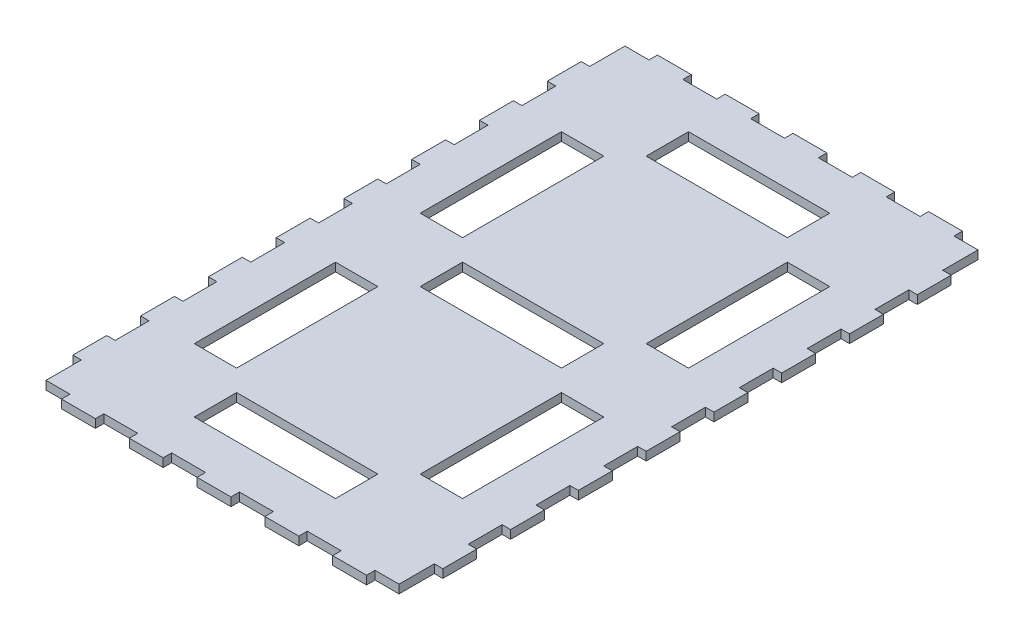
SolidWorks part; units mm, degrees
ref_plane "Front Plane" through (0, 0, 0) normal (0, 0, 1) x (1, 0, 0)
ref_plane "Top Plane" through (0, 0, 0) normal (0, 1, 0) x (1, 0, 0)
ref_plane "Right Plane" through (0, 0, 0) normal (1, 0, 0) x (0, 0, -1)
sketch "Sketch3" plane through (0, 0, 0) normal (0, 1, 0) x (1, 0, 0)
  line L231 (-62.5, -102.5) -> (62.5, -102.5)
  line L232 (-62.5, -102.5) -> (-62.5, 102.5)
  line L233 (-62.5, 102.5) -> (62.5, 102.5)
  line L234 (62.5, -102.5) -> (62.5, 102.5)
  line L235 (-62.5, -102.5) -> (62.5, 102.5) construction
  line L236 (-62.5, 102.5) -> (62.5, -102.5) construction
  point P66 (0, 0)
  dimension "D3" = 205
  dimension "D4" = 125
extrude "Boss-Extrude1" add sketch "Sketch3" along normal blind 3
sketch "Sketch4" plane through (0, 3, 0) normal (0, 1, 0) x (1, 0, 0)
  line L0 (62.5, 102.5) -> (-62.5, 102.5) construction
  line L5 (-32.5, 65) -> (-47.5, 65)
  line L6 (-25, 80) -> (-62.5, 80)
  line L7 (-32.5, 65) -> (-32.5, 15)
  line L8 (-32.5, 15) -> (-47.5, 15)
  line L17 (-25, 87.5) -> (25, 87.5)
  line L18 (-47.5, 65) -> (-47.5, 15)
  line L19 (-25, 87.5) -> (-25, 72.5)
  line L20 (-25, 72.5) -> (25, 72.5)
  line L21 (25, 87.5) -> (25, 72.5)
  line L22 (-62.5, 102.5) -> (-62.5, -102.5) construction
  line L23 (25, 80) -> (62.5, 80)
  line L24 (62.5, -102.5) -> (62.5, 102.5) construction
  line L25 (47.5, 65) -> (47.5, 15)
  line L26 (47.5, 65) -> (32.5, 65)
  line L27 (32.5, 65) -> (32.5, 15)
  line L28 (47.5, 15) -> (32.5, 15)
  line L30 (-25, 7.5) -> (-25, -7.5)
  line L31 (-25, 7.5) -> (25, 7.5)
  line L32 (25, 7.5) -> (25, -7.5)
  line L33 (-25, -7.5) -> (25, -7.5)
  line L34 (-25, -72.5) -> (-25, -87.5)
  line L35 (-25, -72.5) -> (25, -72.5)
  line L36 (25, -72.5) -> (25, -87.5)
  line L37 (-25, -87.5) -> (25, -87.5)
  line L38 (47.5, -15) -> (47.5, -65)
  line L39 (47.5, -15) -> (32.5, -15)
  line L40 (32.5, -15) -> (32.5, -65)
  line L41 (47.5, -65) -> (32.5, -65)
  line L42 (-32.5, -15) -> (-32.5, -65)
  line L43 (-32.5, -15) -> (-47.5, -15)
  line L44 (-47.5, -15) -> (-47.5, -65)
  line L45 (-32.5, -65) -> (-47.5, -65)
  point P16 (0, 87.5)
  dimension "D1" = 15
  dimension "D2" = 37.5
  dimension "D3" = 37.5
  dimension "D4" = 15
  dimension "D6" = 95
  dimension "D7" = 15
  dimension "D8" = 7.5
  dimension "D11" = 15
  dimension "D12" = 7.5
  dimension "D13" = 15
  dimension "D5" = 3
  dimension "D9" = 2
  dimension "D10" = 2
extrude "Cut-Extrude1" cut sketch "Sketch4" against normal blind 6 contours L5 L18 L8 L7 | L28 L25 L26 L27 | L30 L33 L32 L31 | L45 L42 L43 L44 | L41 L38 L39 L40 | L19 L17 L21 L20 | L35 L36 L37 L34
sketch "Sketch5" plane through (0, 3, 0) normal (0, 1, 0) x (1, 0, 0)
  line L0 (62.5, 102.5) -> (-62.5, 102.5) construction
  line L1 (-54, 102.5) -> (-42, 102.5)
  line L2 (-54, 102.5) -> (-54, 105.5)
  line L3 (-54, 105.5) -> (-42, 105.5)
  line L4 (-42, 102.5) -> (-42, 105.5)
  line L5 (-30, 102.5) -> (-30, 105.5)
  line L6 (-30, 102.5) -> (-18, 102.5)
  line L7 (-18, 102.5) -> (-18, 105.5)
  line L8 (-30, 105.5) -> (-18, 105.5)
  line L9 (-6, 102.5) -> (-6, 105.5)
  line L10 (-6, 102.5) -> (6, 102.5)
  line L11 (6, 102.5) -> (6, 105.5)
  line L12 (-6, 105.5) -> (6, 105.5)
  line L13 (18, 102.5) -> (18, 105.5)
  line L14 (18, 102.5) -> (30, 102.5)
  line L15 (30, 102.5) -> (30, 105.5)
  line L16 (18, 105.5) -> (30, 105.5)
  line L17 (42, 102.5) -> (42, 105.5)
  line L18 (42, 102.5) -> (54, 102.5)
  line L19 (54, 102.5) -> (54, 105.5)
  line L20 (42, 105.5) -> (54, 105.5)
  line L41 (-62.5, 102.5) -> (-62.5, -102.5) construction
  line L43 (62.5, -102.5) -> (62.5, 102.5) construction
  line L44 (-62.5, 90) -> (-65.5, 90)
  line L45 (-62.5, 90) -> (-62.5, 78)
  line L46 (-62.5, 78) -> (-65.5, 78)
  line L47 (-65.5, 90) -> (-65.5, 78)
  line L48 (65.5, 90) -> (65.5, 78)
  line L49 (65.5, 90) -> (62.5, 90)
  line L50 (62.5, 90) -> (62.5, 78)
  line L51 (65.5, 78) -> (62.5, 78)
  line L52 (65.5, 66) -> (65.5, 54)
  line L53 (65.5, 66) -> (62.5, 66)
  line L54 (62.5, 66) -> (62.5, 54)
  line L55 (65.5, 54) -> (62.5, 54)
  line L56 (65.5, 42) -> (65.5, 30)
  line L57 (65.5, 42) -> (62.5, 42)
  line L58 (62.5, 42) -> (62.5, 30)
  line L59 (65.5, 30) -> (62.5, 30)
  line L60 (65.5, 18) -> (65.5, 6)
  line L61 (65.5, 18) -> (62.5, 18)
  line L62 (62.5, 18) -> (62.5, 6)
  line L63 (65.5, 6) -> (62.5, 6)
  line L64 (65.5, -6) -> (65.5, -18)
  line L65 (65.5, -6) -> (62.5, -6)
  line L66 (62.5, -6) -> (62.5, -18)
  line L67 (65.5, -18) -> (62.5, -18)
  line L68 (65.5, -30) -> (65.5, -42)
  line L69 (65.5, -30) -> (62.5, -30)
  line L70 (62.5, -30) -> (62.5, -42)
  line L71 (65.5, -42) -> (62.5, -42)
  line L72 (65.5, -54) -> (65.5, -66)
  line L73 (65.5, -54) -> (62.5, -54)
  line L74 (62.5, -54) -> (62.5, -66)
  line L75 (65.5, -66) -> (62.5, -66)
  line L76 (65.5, -78) -> (65.5, -90)
  line L77 (65.5, -78) -> (62.5, -78)
  line L78 (62.5, -78) -> (62.5, -90)
  line L79 (65.5, -90) -> (62.5, -90)
  line L80 (-62.5, 66) -> (-62.5, 54)
  line L81 (-62.5, 66) -> (-65.5, 66)
  line L82 (-65.5, 66) -> (-65.5, 54)
  line L83 (-62.5, 54) -> (-65.5, 54)
  line L84 (-62.5, 42) -> (-62.5, 30)
  line L85 (-62.5, 42) -> (-65.5, 42)
  line L86 (-65.5, 42) -> (-65.5, 30)
  line L87 (-62.5, 30) -> (-65.5, 30)
  line L88 (-62.5, 18) -> (-62.5, 6)
  line L89 (-62.5, 18) -> (-65.5, 18)
  line L90 (-65.5, 18) -> (-65.5, 6)
  line L91 (-62.5, 6) -> (-65.5, 6)
  line L92 (-62.5, -6) -> (-62.5, -18)
  line L93 (-62.5, -6) -> (-65.5, -6)
  line L94 (-65.5, -6) -> (-65.5, -18)
  line L95 (-62.5, -18) -> (-65.5, -18)
  line L96 (-62.5, -30) -> (-62.5, -42)
  line L97 (-62.5, -30) -> (-65.5, -30)
  line L98 (-65.5, -30) -> (-65.5, -42)
  line L99 (-62.5, -42) -> (-65.5, -42)
  line L100 (-62.5, -54) -> (-62.5, -66)
  line L101 (-62.5, -54) -> (-65.5, -54)
  line L102 (-65.5, -54) -> (-65.5, -66)
  line L103 (-62.5, -66) -> (-65.5, -66)
  line L104 (-62.5, -78) -> (-62.5, -90)
  line L105 (-62.5, -78) -> (-65.5, -78)
  line L106 (-65.5, -78) -> (-65.5, -90)
  line L107 (-62.5, -90) -> (-65.5, -90)
  line L108 (-62.5, 6) -> (-62.5, -6)
  line L109 (-54, -105.5) -> (-54, -102.5)
  line L110 (-54, -105.5) -> (-42, -105.5)
  line L111 (-42, -105.5) -> (-42, -102.5)
  line L112 (-54, -102.5) -> (-42, -102.5)
  line L113 (-30, -105.5) -> (-30, -102.5)
  line L114 (-30, -105.5) -> (-18, -105.5)
  line L115 (-18, -105.5) -> (-18, -102.5)
  line L116 (-30, -102.5) -> (-18, -102.5)
  line L117 (-6, -105.5) -> (-6, -102.5)
  line L118 (-6, -105.5) -> (6, -105.5)
  line L119 (6, -105.5) -> (6, -102.5)
  line L120 (-6, -102.5) -> (6, -102.5)
  line L121 (18, -105.5) -> (18, -102.5)
  line L122 (18, -105.5) -> (30, -105.5)
  line L123 (30, -105.5) -> (30, -102.5)
  line L124 (18, -102.5) -> (30, -102.5)
  line L125 (42, -105.5) -> (42, -102.5)
  line L126 (42, -105.5) -> (54, -105.5)
  line L127 (54, -105.5) -> (54, -102.5)
  line L128 (42, -102.5) -> (54, -102.5)
  point P6 (0, 102.5)
  point P55 (-62.5, 0)
  line M6 (62.5, -102.5) -> (62.5, 102.5)
  line M7 (62.5, 102.5) -> (-62.5, 102.5)
  line M8 (-62.5, 102.5) -> (-62.5, -102.5)
  line M9 (-62.5, -102.5) -> (62.5, -102.5)
  dimension "D1" = 12
  dimension "D2" = 3
  dimension "D5" = 12
  dimension "D6" = 205
  dimension "D8" = 12
  dimension "D9" = 3
  dimension "D12" = 125
  dimension "D13" = 24
  dimension "D3" = 5
  dimension "D4" = 2
  dimension "D10" = 2
  dimension "D11" = 8
extrude "Boss-Extrude2" add sketch "Sketch5" against normal blind 3 contours L122 L123 L121 M9 | L118 L119 L117 M9 | L107 L105 L106 M8 | L103 L101 L102 M8 | L95 L93 L94 M8 | L79 L76 L77 M6 | L71 L68 L69 M6 | L67 L64 L65 M6 | L63 L60 L61 M6 | L59 L56 L57 M6 | L51 L48 L49 M6 | L16 L13 L15 M7 | L12 L9 L11 M7 | L8 L5 L7 M7 | L4 L3 L2 M7 | L87 L85 L86 M8 | L91 L89 L90 M8 | L128 L127 L126 L125 | L116 L115 L114 L113 | L112 L111 L110 L109 | L98 L99 L96 L97 | L74 L75 L72 L73 | L52 L55 L54 L53 | L20 L19 L18 L17 | L45 L46 L47 L44 | L82 L83 L80 L81
